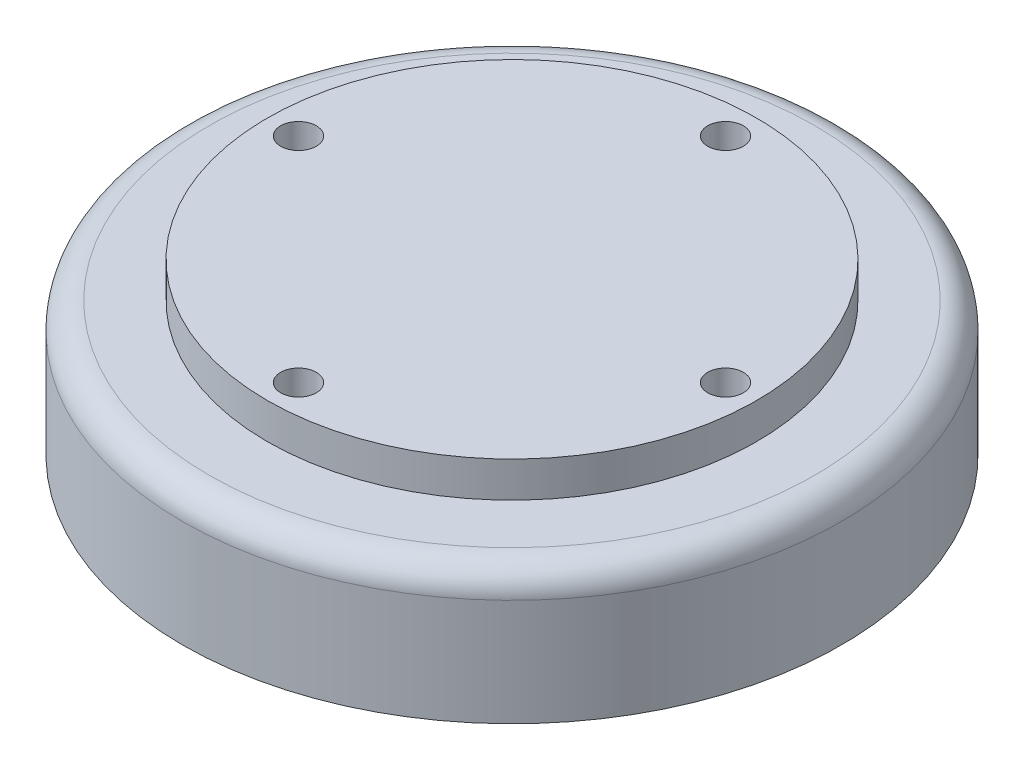
SolidWorks part; units mm, degrees
ref_plane "Front Plane" through (0, 0, 0) normal (0, 0, 1) x (1, 0, 0)
ref_plane "Top Plane" through (0, 0, 0) normal (0, 1, 0) x (1, 0, 0)
ref_plane "Right Plane" through (0, 0, 0) normal (1, 0, 0) x (0, 0, -1)
sketch "Sketch2" plane through (0, 0, 0) normal (0, 1, 0) x (1, 0, 0)
  circle A0 centre (0, 0) radius 27.469
  dimension "D1" = 54.938
extrude "Boss-Extrude1" add sketch "Sketch2" along normal blind 4
sketch "Sketch3" plane through (0, 4, 0) normal (0, 1, 0) x (1, 0, 0)
  circle A1 centre (-23.971, 0) radius 2
  circle A2 centre (0, 23.971) radius 2
  circle A3 centre (23.971, 0) radius 2
  circle A4 centre (0, -23.971) radius 2
  point P14 (0, 0)
  dimension "D2" = 4
  dimension "D1" = 4
extrude "Cut-Extrude1" cut sketch "Sketch3" against normal through all
sketch "Sketch4" plane through (0, 0, 0) normal (0, -1, 0) x (1, 0, 0)
  circle A0 centre (0, 0) radius 37
  dimension "D1" = 74
extrude "Boss-Extrude2" add sketch "Sketch4" along normal blind 15
sketch "Sketch6" plane through (0, -15, 0) normal (0, -1, 0) x (1, 0, 0)
  line L1 (-29.3698, 13.5184) -> (-26.3922, -18.6758)
  line L2 (-26.3922, -18.6758) -> (2.9777, -32.1942)
  line L3 (2.9777, -32.1942) -> (29.3698, -13.5184)
  line L4 (29.3698, -13.5184) -> (26.3922, 18.6758)
  line L5 (26.3922, 18.6758) -> (-2.9777, 32.1942)
  line L6 (-2.9777, 32.1942) -> (-29.3698, 13.5184)
  arc A0 (11.7072, 25.435) -> (-16.1738, 22.8563) centre (0, 0) ccw construction
  dimension "D1" = 56
extrude "Cut-Extrude3" cut sketch "Sketch6" against normal blind 8
fillet "Fillet1" radius 3 1 edges at (0, 0, -37)
ref_plane "Plane1" through (0, 9, 0) normal (0, 1, 0) x (1, 0, 0)
sketch "Sketch7" plane through (0, 9, 0) normal (0, 1, 0) x (1, 0, 0)
  circle A0 centre (0, 23.971) radius 2 construction
  circle A1 centre (23.971, 0) radius 2 construction
  circle A2 centre (0, -23.971) radius 2 construction
  circle A3 centre (-23.971, 0) radius 2 construction
  circle A4 centre (0, 23.971) radius 2
  circle A5 centre (23.971, 0) radius 2
  circle A6 centre (0, -23.971) radius 2
  circle A7 centre (-23.971, 0) radius 2
extrude "Cut-Extrude5" cut sketch "Sketch7" against normal through all
